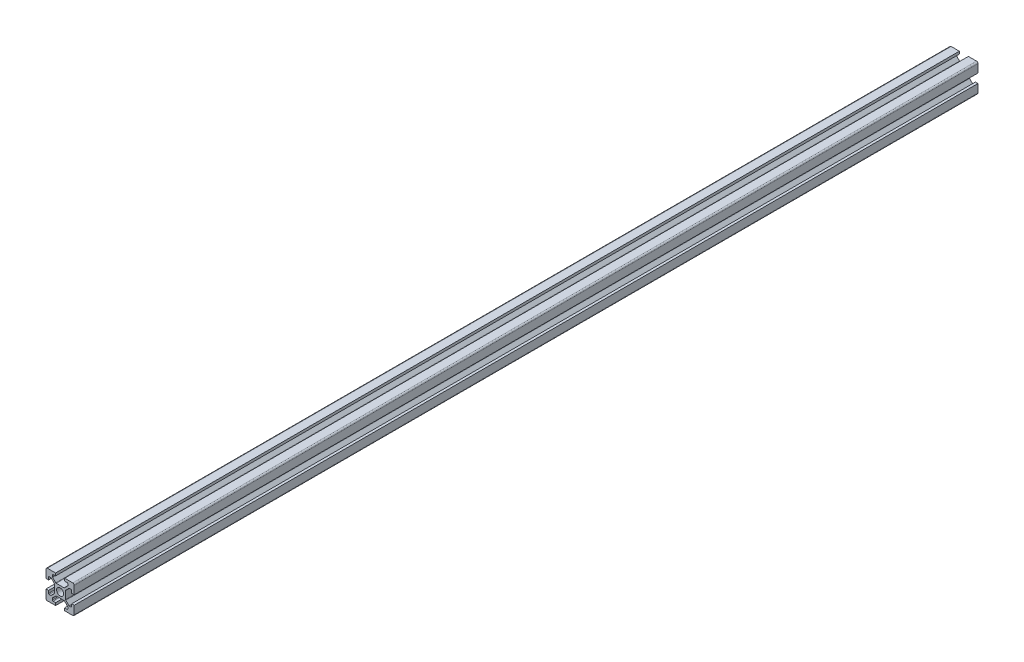
SolidWorks part; units mm, degrees
material "1060 Alloy"
ref_plane "Front Plane" through (0, 0, 0) normal (0, 0, 1) x (1, 0, 0)
ref_plane "Top Plane" through (0, 0, 0) normal (0, 1, 0) x (1, 0, 0)
ref_plane "Right Plane" through (0, 0, 0) normal (1, 0, 0) x (0, 0, -1)
sketch "Sketch1" plane through (0, 0, 0) normal (0, 0, 1) x (1, 0, 0)
  line L0 (20, 0) -> (-8.059, 28.059) construction
  line L1 (0, 0) -> (6.8, 0)
  line L2 (0, 0) -> (0, 6.8)
  line L3 (0, 20) -> (6.8, 20)
  line L4 (20, 0) -> (20, 6.8)
  line L5 (6.8, 20) -> (6.8, 18.2)
  line L6 (20, 20) -> (8.2322, 8.2322) construction
  line L7 (12.95, 6.1) -> (7.05, 6.1)
  line L8 (13.9, 7.05) -> (13.9, 12.95)
  line L9 (12.95, 13.9) -> (7.05, 13.9)
  line L10 (6.1, 7.05) -> (6.1, 12.95)
  line L11 (13.9, 6.1) -> (6.1, 13.9) construction
  line L12 (13.9, 13.9) -> (6.1, 6.1) construction
  line L13 (4.55, 16.4) -> (7.05, 13.9)
  line L14 (13.2, 18.2) -> (13.2, 20)
  line L15 (1.8, 6.8) -> (0, 6.8)
  line L16 (0, 13.2) -> (0, 20)
  line L17 (0, 13.2) -> (1.8, 13.2)
  line L18 (10, 10) -> (10, 13.9) construction
  line L19 (16.4, 4.55) -> (13.9, 7.05)
  line L20 (4.55, 16.4) -> (4.55, 18.2)
  line L21 (4.55, 18.2) -> (6.8, 18.2)
  line L22 (13.2, 18.2) -> (15.45, 18.2)
  line L23 (15.45, 18.2) -> (15.45, 16.4)
  line L24 (15.45, 16.4) -> (12.95, 13.9)
  line L25 (16.4, 4.55) -> (18.2, 4.55)
  line L26 (18.2, 4.55) -> (18.2, 6.8)
  line L27 (20, 6.8) -> (18.2, 6.8)
  line L28 (18.2, 13.2) -> (20, 13.2)
  line L29 (18.2, 13.2) -> (18.2, 15.45)
  line L30 (18.2, 15.45) -> (16.4, 15.45)
  line L31 (16.4, 15.45) -> (13.9, 12.95)
  line L32 (1.8, 4.55) -> (3.6, 4.55)
  line L33 (3.6, 15.45) -> (6.1, 12.95)
  line L34 (3.6, 15.45) -> (1.8, 15.45)
  line L35 (1.8, 15.45) -> (1.8, 13.2)
  line L36 (0, 13.2) -> (1.8, 13.2)
  line L37 (1.8, 6.8) -> (0, 6.8)
  line L38 (3.6, 4.55) -> (6.1, 7.05)
  line L39 (1.8, 6.8) -> (1.8, 4.55)
  line L40 (15.45, 3.6) -> (12.95, 6.1)
  line L41 (4.55, 3.6) -> (7.05, 6.1)
  line L42 (4.55, 1.8) -> (4.55, 3.6)
  line L43 (6.8, 1.8) -> (4.55, 1.8)
  line L44 (6.8, 1.8) -> (6.8, 0)
  line L45 (15.45, 3.6) -> (15.45, 1.8)
  line L46 (15.45, 1.8) -> (13.2, 1.8)
  line L47 (13.2, 0) -> (13.2, 1.8)
  line L48 (13.2, 20) -> (20, 20)
  line L49 (20, 13.2) -> (20, 20)
  line L50 (13.2, 0) -> (20, 0)
  line L51 (6.1, 6.1) -> (-5.5045, -5.5045) construction
  circle A0 centre (10, 10) radius 2.5
  point P25 (10, 16.4)
  point P39 (13.2, 19.1)
  point P46 (0.9, 6.8)
  dimension "D3" = 5
  dimension "D2" = 20
  dimension "D4" = 7.8
  dimension "D5" = 7.8
  dimension "D6" = 6.8
  dimension "D7" = 6.8
  dimension "D8" = 1.8
  dimension "D9" = 10.9
  dimension "D10" = 1.8
  dimension "D11" = 10.9
  dimension "D12" = 20
extrude "Boss-Extrude1" add sketch "Sketch1" along normal blind 300 contours L47 L50 L4 L27 L26 L25 L19 L8 L31 L30 L29 L28 L49 L48 L14 L22 L23 L24 L9 L13 L20 L21 L5 L3 L16 L17 L35 L34 L33 L10 L38 L32 L39 L15 L2 L1 L44 L43 L42 L41 L7 L40 L45 L46 A0
fillet "Fillet1" radius 1 4 edges at (20, 20, 150) (20, 0, 150) (0, 0, 150) (0, 20, 150)
fillet "Fillet2" radius 0.5 6 edges at (4.55, 18.2, 150) (4.55, 16.4, 150) (7.05, 13.9, 150) (15.45, 18.2, 150) (15.45, 16.4, 150) (12.95, 13.9, 150)
fillet "Fillet3" radius 0.5 6 edges at (18.2, 15.45, 150) (16.4, 15.45, 150) (13.9, 12.95, 150) (18.2, 4.55, 150) (13.9, 7.05, 150) (16.4, 4.55, 150)
fillet "Fillet4" radius 0.5 6 edges at (1.8, 15.45, 150) (3.6, 15.45, 150) (6.1, 12.95, 150) (3.6, 4.55, 150) (1.8, 4.55, 150) (6.1, 7.05, 150)
fillet "Fillet5" radius 0.5 6 edges at (7.05, 6.1, 150) (4.55, 3.6, 150) (4.55, 1.8, 150) (15.45, 1.8, 150) (15.45, 3.6, 150) (12.95, 6.1, 150)
sketch "Sketch4" plane through (0, 0, 0) normal (0, 0, -1) x (-1, 0, 0)
  line L44 (-13.2, 20) -> (-19, 20)
  line L45 (-20, 19) -> (-20, 13.2)
  line L46 (-20, 13.2) -> (-18.2, 13.2)
  line L47 (-18.2, 13.2) -> (-18.2, 14.95)
  line L48 (-17.7, 15.45) -> (-16.6071, 15.45)
  line L49 (-16.2536, 15.3036) -> (-14.0464, 13.0964)
  line L50 (-13.9, 12.7429) -> (-13.9, 7.2571)
  line L51 (-14.0464, 6.9036) -> (-16.2536, 4.6964)
  line L52 (-16.6071, 4.55) -> (-17.7, 4.55)
  line L53 (-18.2, 5.05) -> (-18.2, 6.8)
  line L54 (-18.2, 6.8) -> (-20, 6.8)
  line L55 (-20, 6.8) -> (-20, 1)
  line L56 (-19, 0) -> (-13.2, 0)
  line L57 (-13.2, 0) -> (-13.2, 1.8)
  line L58 (-13.2, 1.8) -> (-14.95, 1.8)
  line L59 (-15.45, 2.3) -> (-15.45, 3.3929)
  line L60 (-15.3036, 3.7464) -> (-13.0964, 5.9536)
  line L61 (-12.7429, 6.1) -> (-7.2571, 6.1)
  line L62 (-6.9036, 5.9536) -> (-4.6964, 3.7464)
  line L63 (-4.55, 3.3929) -> (-4.55, 2.3)
  line L64 (-5.05, 1.8) -> (-6.8, 1.8)
  line L65 (-6.8, 1.8) -> (-6.8, 0)
  line L66 (-6.8, 0) -> (-1, 0)
  line L67 (0, 1) -> (0, 6.8)
  line L68 (0, 6.8) -> (-1.8, 6.8)
  line L69 (-1.8, 6.8) -> (-1.8, 5.05)
  line L70 (-2.3, 4.55) -> (-3.3929, 4.55)
  line L71 (-3.7464, 4.6964) -> (-5.9536, 6.9036)
  line L72 (-6.1, 7.2571) -> (-6.1, 12.7429)
  line L73 (-5.9536, 13.0964) -> (-3.7464, 15.3036)
  line L74 (-3.3929, 15.45) -> (-2.3, 15.45)
  line L75 (-1.8, 14.95) -> (-1.8, 13.2)
  line L76 (-1.8, 13.2) -> (0, 13.2)
  line L77 (0, 13.2) -> (0, 19)
  line L78 (-1, 20) -> (-6.8, 20)
  line L79 (-6.8, 20) -> (-6.8, 18.2)
  line L80 (-6.8, 18.2) -> (-5.05, 18.2)
  line L81 (-4.55, 17.7) -> (-4.55, 16.6071)
  line L82 (-4.6964, 16.2536) -> (-6.9036, 14.0464)
  line L83 (-7.2571, 13.9) -> (-12.7429, 13.9)
  line L84 (-13.0964, 14.0464) -> (-15.3036, 16.2536)
  line L85 (-15.45, 16.6071) -> (-15.45, 17.7)
  line L86 (-14.95, 18.2) -> (-13.2, 18.2)
  line L87 (-13.2, 18.2) -> (-13.2, 20)
  line L88 (-13.2, 20) -> (-19, 20)
  line L89 (-20, 19) -> (-20, 13.2)
  line L90 (-20, 13.2) -> (-18.2, 13.2)
  line L91 (-18.2, 13.2) -> (-18.2, 14.95)
  line L92 (-17.7, 15.45) -> (-16.6071, 15.45)
  line L93 (-16.2536, 15.3036) -> (-14.0464, 13.0964)
  line L94 (-13.9, 12.7429) -> (-13.9, 7.2571)
  line L95 (-14.0464, 6.9036) -> (-16.2536, 4.6964)
  line L96 (-16.6071, 4.55) -> (-17.7, 4.55)
  line L97 (-18.2, 5.05) -> (-18.2, 6.8)
  line L98 (-18.2, 6.8) -> (-20, 6.8)
  line L99 (-20, 6.8) -> (-20, 1)
  line L100 (-19, 0) -> (-13.2, 0)
  line L101 (-13.2, 0) -> (-13.2, 1.8)
  line L102 (-13.2, 1.8) -> (-14.95, 1.8)
  line L103 (-15.45, 2.3) -> (-15.45, 3.3929)
  line L104 (-15.3036, 3.7464) -> (-13.0964, 5.9536)
  line L105 (-12.7429, 6.1) -> (-7.2571, 6.1)
  line L106 (-6.9036, 5.9536) -> (-4.6964, 3.7464)
  line L107 (-4.55, 3.3929) -> (-4.55, 2.3)
  line L108 (-5.05, 1.8) -> (-6.8, 1.8)
  line L109 (-6.8, 1.8) -> (-6.8, 0)
  line L110 (-6.8, 0) -> (-1, 0)
  line L111 (0, 1) -> (0, 6.8)
  line L112 (0, 6.8) -> (-1.8, 6.8)
  line L113 (-1.8, 6.8) -> (-1.8, 5.05)
  line L114 (-2.3, 4.55) -> (-3.3929, 4.55)
  line L115 (-3.7464, 4.6964) -> (-5.9536, 6.9036)
  line L116 (-6.1, 7.2571) -> (-6.1, 12.7429)
  line L117 (-5.9536, 13.0964) -> (-3.7464, 15.3036)
  line L118 (-3.3929, 15.45) -> (-2.3, 15.45)
  line L119 (-1.8, 14.95) -> (-1.8, 13.2)
  line L120 (-1.8, 13.2) -> (0, 13.2)
  line L121 (0, 13.2) -> (0, 19)
  line L122 (-1, 20) -> (-6.8, 20)
  line L123 (-6.8, 20) -> (-6.8, 18.2)
  line L124 (-6.8, 18.2) -> (-5.05, 18.2)
  line L125 (-4.55, 17.7) -> (-4.55, 16.6071)
  line L126 (-4.6964, 16.2536) -> (-6.9036, 14.0464)
  line L127 (-7.2571, 13.9) -> (-12.7429, 13.9)
  line L128 (-13.0964, 14.0464) -> (-15.3036, 16.2536)
  line L129 (-15.45, 16.6071) -> (-15.45, 17.7)
  line L130 (-14.95, 18.2) -> (-13.2, 18.2)
  line L131 (-13.2, 18.2) -> (-13.2, 20)
  arc A28 (-19, 20) -> (-20, 19) centre (-19, 19) ccw
  arc A29 (-17.7, 15.45) -> (-18.2, 14.95) centre (-17.7, 14.95) ccw
  arc A30 (-16.2536, 15.3036) -> (-16.6071, 15.45) centre (-16.6071, 14.95) ccw
  arc A31 (-13.9, 12.7429) -> (-14.0464, 13.0964) centre (-14.4, 12.7429) ccw
  arc A32 (-14.0464, 6.9036) -> (-13.9, 7.2571) centre (-14.4, 7.2571) ccw
  arc A33 (-16.6071, 4.55) -> (-16.2536, 4.6964) centre (-16.6071, 5.05) ccw
  arc A34 (-18.2, 5.05) -> (-17.7, 4.55) centre (-17.7, 5.05) ccw
  arc A35 (-20, 1) -> (-19, 0) centre (-19, 1) ccw
  arc A36 (-15.45, 2.3) -> (-14.95, 1.8) centre (-14.95, 2.3) ccw
  arc A37 (-15.3036, 3.7464) -> (-15.45, 3.3929) centre (-14.95, 3.3929) ccw
  arc A38 (-12.7429, 6.1) -> (-13.0964, 5.9536) centre (-12.7429, 5.6) ccw
  arc A39 (-6.9036, 5.9536) -> (-7.2571, 6.1) centre (-7.2571, 5.6) ccw
  arc A40 (-4.55, 3.3929) -> (-4.6964, 3.7464) centre (-5.05, 3.3929) ccw
  arc A41 (-5.05, 1.8) -> (-4.55, 2.3) centre (-5.05, 2.3) ccw
  arc A42 (-1, 0) -> (0, 1) centre (-1, 1) ccw
  arc A43 (-2.3, 4.55) -> (-1.8, 5.05) centre (-2.3, 5.05) ccw
  arc A44 (-3.7464, 4.6964) -> (-3.3929, 4.55) centre (-3.3929, 5.05) ccw
  arc A45 (-6.1, 7.2571) -> (-5.9536, 6.9036) centre (-5.6, 7.2571) ccw
  arc A46 (-5.9536, 13.0964) -> (-6.1, 12.7429) centre (-5.6, 12.7429) ccw
  arc A47 (-3.3929, 15.45) -> (-3.7464, 15.3036) centre (-3.3929, 14.95) ccw
  arc A48 (-1.8, 14.95) -> (-2.3, 15.45) centre (-2.3, 14.95) ccw
  arc A49 (0, 19) -> (-1, 20) centre (-1, 19) ccw
  arc A50 (-4.55, 17.7) -> (-5.05, 18.2) centre (-5.05, 17.7) ccw
  arc A51 (-4.6964, 16.2536) -> (-4.55, 16.6071) centre (-5.05, 16.6071) ccw
  arc A52 (-7.2571, 13.9) -> (-6.9036, 14.0464) centre (-7.2571, 14.4) ccw
  arc A53 (-13.0964, 14.0464) -> (-12.7429, 13.9) centre (-12.7429, 14.4) ccw
  arc A54 (-15.45, 16.6071) -> (-15.3036, 16.2536) centre (-14.95, 16.6071) ccw
  arc A55 (-14.95, 18.2) -> (-15.45, 17.7) centre (-14.95, 17.7) ccw
  arc A56 (-19, 20) -> (-20, 19) centre (-19, 19) ccw
  arc A57 (-17.7, 15.45) -> (-18.2, 14.95) centre (-17.7, 14.95) ccw
  arc A58 (-16.2536, 15.3036) -> (-16.6071, 15.45) centre (-16.6071, 14.95) ccw
  arc A59 (-13.9, 12.7429) -> (-14.0464, 13.0964) centre (-14.4, 12.7429) ccw
  arc A60 (-14.0464, 6.9036) -> (-13.9, 7.2571) centre (-14.4, 7.2571) ccw
  arc A61 (-16.6071, 4.55) -> (-16.2536, 4.6964) centre (-16.6071, 5.05) ccw
  arc A62 (-18.2, 5.05) -> (-17.7, 4.55) centre (-17.7, 5.05) ccw
  arc A63 (-20, 1) -> (-19, 0) centre (-19, 1) ccw
  arc A64 (-15.45, 2.3) -> (-14.95, 1.8) centre (-14.95, 2.3) ccw
  arc A65 (-15.3036, 3.7464) -> (-15.45, 3.3929) centre (-14.95, 3.3929) ccw
  arc A66 (-12.7429, 6.1) -> (-13.0964, 5.9536) centre (-12.7429, 5.6) ccw
  arc A67 (-6.9036, 5.9536) -> (-7.2571, 6.1) centre (-7.2571, 5.6) ccw
  arc A68 (-4.55, 3.3929) -> (-4.6964, 3.7464) centre (-5.05, 3.3929) ccw
  arc A69 (-5.05, 1.8) -> (-4.55, 2.3) centre (-5.05, 2.3) ccw
  arc A70 (-1, 0) -> (0, 1) centre (-1, 1) ccw
  arc A71 (-2.3, 4.55) -> (-1.8, 5.05) centre (-2.3, 5.05) ccw
  arc A72 (-3.7464, 4.6964) -> (-3.3929, 4.55) centre (-3.3929, 5.05) ccw
  arc A73 (-6.1, 7.2571) -> (-5.9536, 6.9036) centre (-5.6, 7.2571) ccw
  arc A74 (-5.9536, 13.0964) -> (-6.1, 12.7429) centre (-5.6, 12.7429) ccw
  arc A75 (-3.3929, 15.45) -> (-3.7464, 15.3036) centre (-3.3929, 14.95) ccw
  arc A76 (-1.8, 14.95) -> (-2.3, 15.45) centre (-2.3, 14.95) ccw
  arc A77 (0, 19) -> (-1, 20) centre (-1, 19) ccw
  arc A78 (-4.55, 17.7) -> (-5.05, 18.2) centre (-5.05, 17.7) ccw
  arc A79 (-4.6964, 16.2536) -> (-4.55, 16.6071) centre (-5.05, 16.6071) ccw
  arc A80 (-7.2571, 13.9) -> (-6.9036, 14.0464) centre (-7.2571, 14.4) ccw
  arc A81 (-13.0964, 14.0464) -> (-12.7429, 13.9) centre (-12.7429, 14.4) ccw
  arc A82 (-15.45, 16.6071) -> (-15.3036, 16.2536) centre (-14.95, 16.6071) ccw
  arc A83 (-14.95, 18.2) -> (-15.45, 17.7) centre (-14.95, 17.7) ccw
  dimension "D1" = 0
extrude "Boss-Extrude2" add sketch "Sketch4" along normal blind 340
